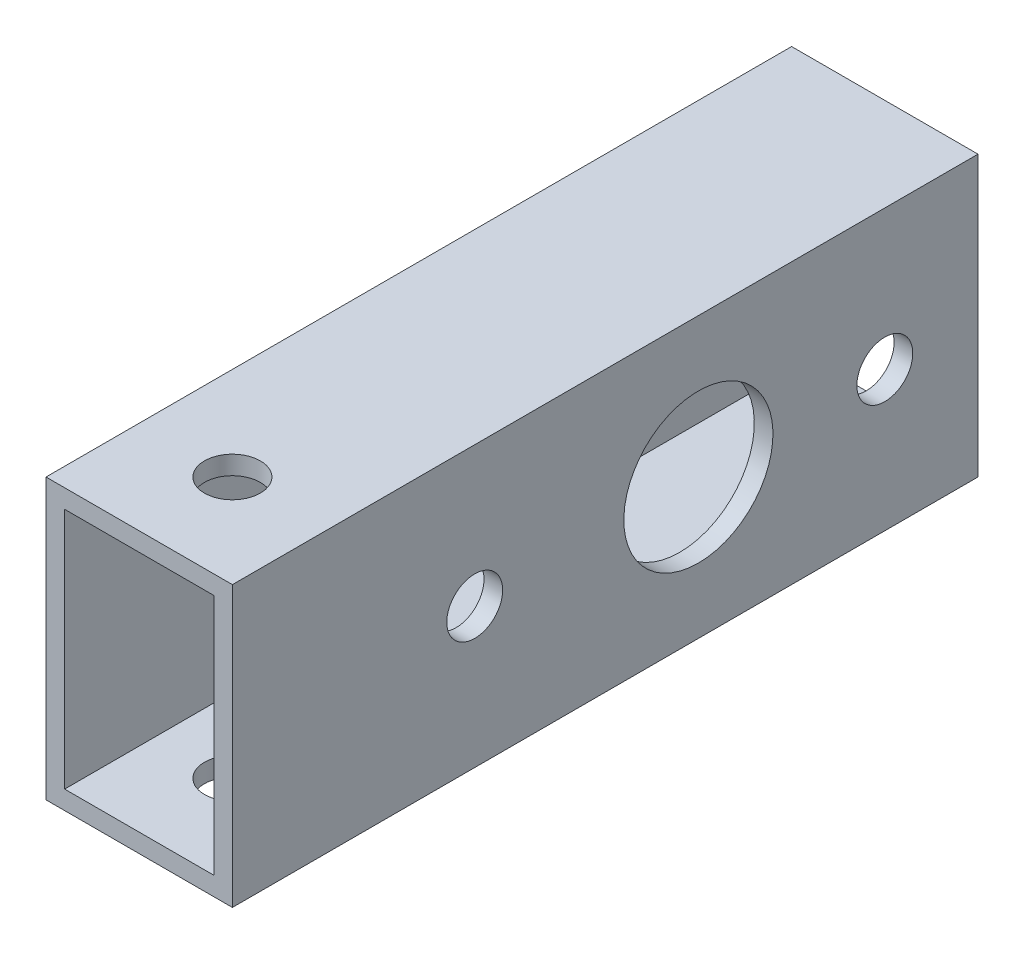
SolidWorks part; units mm, degrees
material "6063-O"
ref_plane "前视基准面" through (0, 0, 0) normal (0, 0, 1) x (1, 0, 0)
ref_plane "上视基准面" through (0, 0, 0) normal (0, 1, 0) x (1, 0, 0)
ref_plane "右视基准面" through (0, 0, 0) normal (1, 0, 0) x (0, 0, -1)
other "Configuration Table"
sketch "草图1" plane through (0, 0, 0) normal (0, 0, 1) x (1, 0, 0)
  line L1 (93.1003, 55.9367) -> (83.1003, 55.9367)
  line L2 (93.1003, 55.9367) -> (93.1003, 40.9367)
  line L3 (93.1003, 40.9367) -> (83.1003, 40.9367)
  line L4 (83.1003, 55.9367) -> (83.1003, 40.9367)
  line L5 (93.1003, 55.9367) -> (83.1003, 40.9367) construction
  line L6 (93.1003, 40.9367) -> (83.1003, 55.9367) construction
  point P4 (88.1003, 48.4367)
  dimension "D1" = 10
  dimension "D2" = 15
extrude "拉伸-薄壁1" add sketch "草图1" along normal blind 40 thin thin type one direction reverse wall 1
sketch "草图2" plane through (83.1003, 0, 0) normal (-1, 0, 0) x (0, 0, 1)
  line L0 (0, 48.4367) -> (40, 48.4367) construction
  line L1 (0, 55.9367) -> (0, 40.9367) construction
  line L3 (40, 55.9367) -> (40, 40.9367) construction
  circle A0 centre (5, 48.4367) radius 1.5
  circle A1 centre (27, 48.4367) radius 1.5
  circle A2 centre (15, 48.4367) radius 4
  dimension "D2" = 3
  dimension "D3" = 13
  dimension "D4" = 8
  dimension "D5" = 15
  dimension "D1" = 5
extrude "切除-拉伸1" cut sketch "草图2" against normal through all
sketch "草图3" plane through (0, 40.9367, 0) normal (0, -1, 0) x (1, 0, 0)
  line L0 (88.1003, 40) -> (88.1003, 0) construction
  line L1 (83.1003, 40) -> (93.1003, 40) construction
  line L2 (83.1003, 0) -> (93.1003, 0) construction
  circle A0 centre (88.1003, 35) radius 1.5
  dimension "D1" = 3
  dimension "D2" = 35
extrude "切除-拉伸2" cut sketch "草图3" against normal through all
